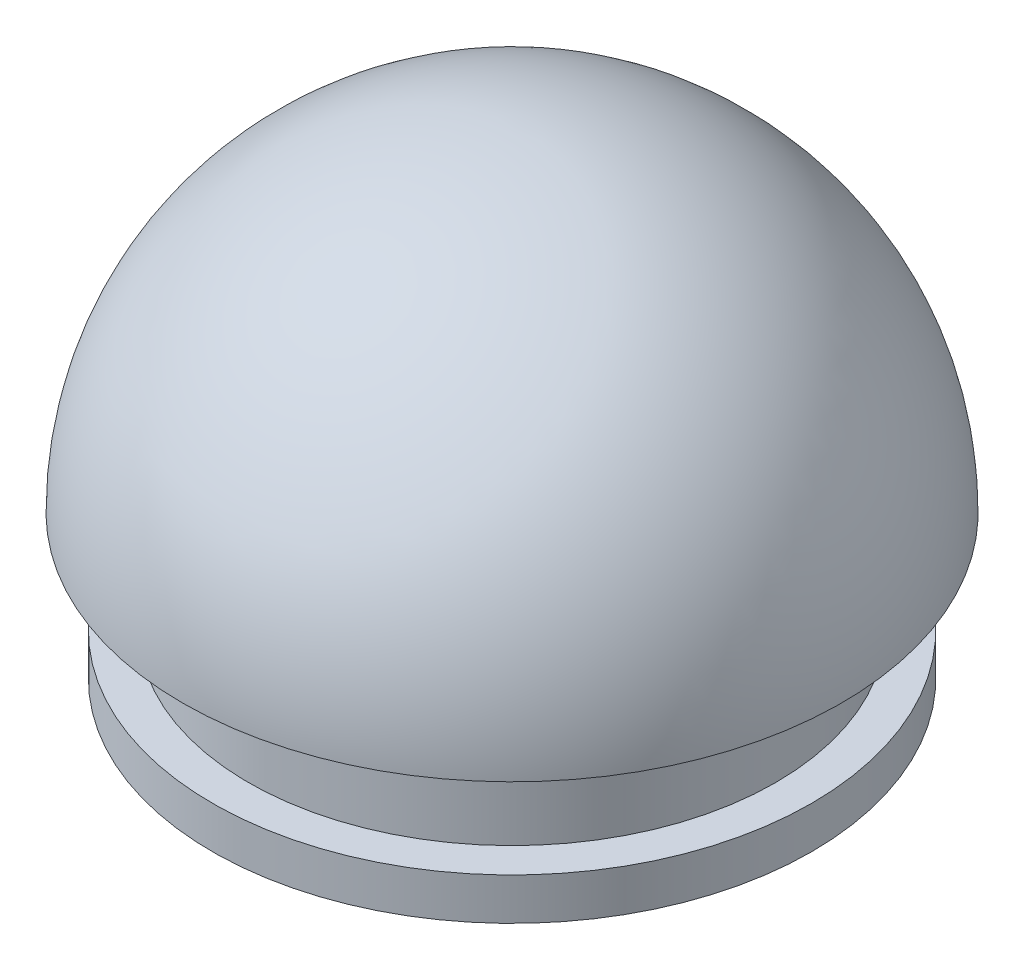
SolidWorks part; units mm, degrees
material "ABS"
ref_plane "Front Plane" through (0, 0, 0) normal (0, 0, 1) x (1, 0, 0)
ref_plane "Top Plane" through (0, 0, 0) normal (0, 1, 0) x (1, 0, 0)
ref_plane "Right Plane" through (0, 0, 0) normal (1, 0, 0) x (0, 0, -1)
sketch "Sketch1" plane through (0, 0, 0) normal (0, 1, 0) x (1, 0, 0)
  line L0 (-0.9963, 27.4819) -> (0.9963, -27.4819)
  arc A0 (0.9963, -27.4819) -> (-0.9963, 27.4819) centre (0, 0) ccw
  dimension "D1" = 55
revolve "Revolve1" add sketch "Sketch1" angle 180 about L0
sketch "Sketch2" plane through (0, 0, 0) normal (0, -1, 0) x (1, 0, 0)
  line L0 (0, 25) -> (0, -25)
  arc A0 (0, -25) -> (0, 25) centre (0, 0) ccw
  dimension "D1" = 50
revolve "Cut-Revolve1" cut sketch "Sketch2" angle 360 about L0
sketch "Sketch3" plane through (0, 0, 0) normal (0, -1, 0) x (1, 0, 0)
  circle A0 centre (0, 0) radius 25.4577
extrude "Boss-Extrude1" add sketch "Sketch3" against normal blind 5
sketch "Sketch4" plane through (0, 0, 0) normal (0, -1, 0) x (1, 0, 0)
  circle A0 centre (0, 0) radius 22
  dimension "D1" = 44
extrude "Boss-Extrude2" add sketch "Sketch4" along normal blind 12
sketch "Sketch5" plane through (0, -12, 0) normal (0, -1, 0) x (1, 0, 0)
  circle A0 centre (0, 0) radius 25
  dimension "D1" = 50
extrude "Boss-Extrude3" add sketch "Sketch5" against normal blind 3.5
sketch "Sketch6" plane through (0, -12, 0) normal (0, -1, 0) x (1, 0, 0)
  circle A0 centre (0, 0) radius 19.5
  dimension "D1" = 39
extrude "Cut-Extrude1" cut sketch "Sketch6" against normal blind 17
